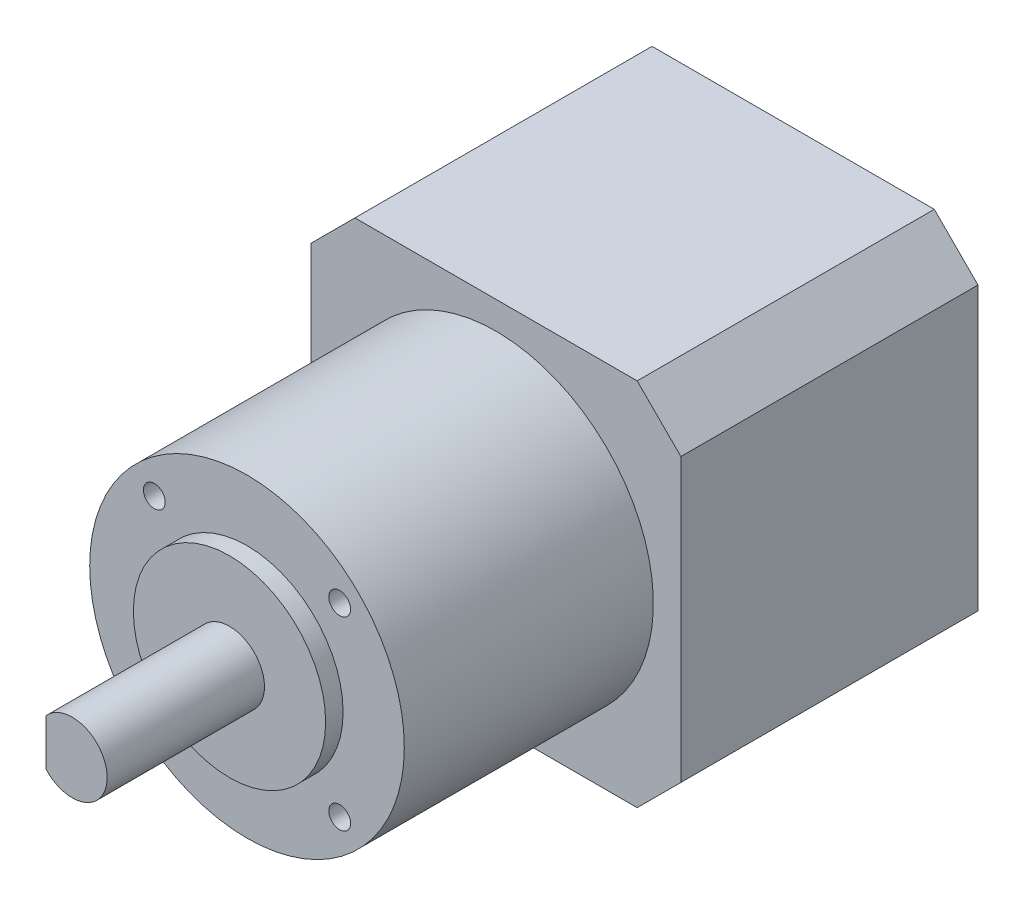
SolidWorks part; units mm, degrees
ref_plane "前视基准面" through (0, 0, 0) normal (0, 0, 1) x (1, 0, 0)
ref_plane "上视基准面" through (0, 0, 0) normal (0, 1, 0) x (1, 0, 0)
ref_plane "右视基准面" through (0, 0, 0) normal (1, 0, 0) x (0, 0, -1)
sketch "草图1" plane through (0, 0, 0) normal (0, 0, 1) x (1, 0, 0)
  line L0 (-21.15, 16.15) -> (-16.15, 21.15)
  line L1 (-16.15, -21.15) -> (16.15, -21.15)
  line L2 (-21.15, -16.15) -> (-21.15, 16.15)
  line L3 (-16.15, 21.15) -> (16.15, 21.15)
  line L4 (21.15, -16.15) -> (21.15, 16.15)
  line L5 (-21.15, -21.15) -> (21.15, 21.15) construction
  line L6 (-21.15, 21.15) -> (21.15, -21.15) construction
  line L7 (16.15, 21.15) -> (21.15, 16.15)
  line L8 (-21.15, -16.15) -> (-16.15, -21.15)
  line L9 (16.15, -21.15) -> (21.15, -16.15)
  point P0 (0, 0)
  dimension "D1" = 42.3
extrude "凸台-拉伸1" add sketch "草图1" along normal blind 34
sketch "草图2" plane through (0, 0, 34) normal (0, 0, 1) x (1, 0, 0)
  circle A0 centre (0, 0) radius 18
  dimension "D1" = 36
extrude "凸台-拉伸2" add sketch "草图2" along normal blind 28.5
sketch "草图3" plane through (0, 0, 62.5) normal (0, 0, 1) x (1, 0, 0)
  circle A0 centre (0, 0) radius 11
  dimension "D1" = 22
extrude "凸台-拉伸3" add sketch "草图3" along normal blind 2
sketch "草图4" plane through (0, 0, 64.5) normal (0, 0, 1) x (1, 0, 0)
  circle A0 centre (0, 0) radius 4
  dimension "D1" = 8
extrude "凸台-拉伸4" add sketch "草图4" along normal blind 18
sketch "草图5" plane through (0, 0, 82.5) normal (0, 0, 1) x (1, 0, 0)
  line L0 (-3, 5.3779) -> (-3, -8.0729)
  line L1 (-3, -8.0729) -> (-11.0943, -8.0729)
  line L2 (-11.0943, -8.0729) -> (-11.0943, 5.3779)
  line L3 (-11.0943, 5.3779) -> (-3, 5.3779)
  dimension "D1" = 3
extrude "切除-拉伸1" cut sketch "草图5" against normal blind 15
sketch "草图6" plane through (0, 0, 62.5) normal (0, 0, 1) x (1, 0, 0)
  line L0 (-10.6066, 10.6066) -> (10.6066, 10.6066) construction
  line L1 (10.6066, 10.6066) -> (10.6066, -10.6066) construction
  line L2 (10.6066, -10.6066) -> (-10.6066, -10.6066) construction
  line L3 (-10.6066, -10.6066) -> (-10.6066, 10.6066) construction
  line L4 (-10.6066, 10.6066) -> (10.6066, -10.6066) construction
  circle A0 centre (-10.6066, 10.6066) radius 1
  circle A1 centre (10.6066, 10.6066) radius 1
  circle A2 centre (-10.6066, -10.6066) radius 1
  circle A3 centre (10.6066, -10.6066) radius 1
  dimension "D2" = 2
  dimension "D1" = 30
extrude "切除-拉伸2" cut sketch "草图6" against normal blind 5
hole_wizard "M3 螺纹孔1" positions "草图7" profile "草图8" tap size "M3" standard "GB"
sketch "草图7" plane through (0, 0, 62.5) normal (0, 0, 1) x (1, 0, 0)
  point P0 (-10.6066, 10.6066)
  point P3 (10.6066, 10.6066)
  point P6 (-10.6066, -10.6066)
  point P9 (10.6066, -10.6066)
cosmetic thread "孔螺蚊线1" parameters "D1"=6, "D2"=3
cosmetic thread "孔螺蚊线2" parameters "D1"=6, "D2"=3
cosmetic thread "孔螺蚊线3" parameters "D1"=6, "D2"=3
cosmetic thread "孔螺蚊线4" parameters "D1"=6, "D2"=3
sketch "草图8" plane through (-10.6066, 10.6066, 62.5) normal (1, 0, 0) x (0, -1, 0)
  line L0 (0, 0) -> (0, 8.2511)
  line L1 (0, 8.2511) -> (1.25, 7.5)
  line L2 (1.25, 7.5) -> (1.25, 0)
  line L5 (1.25, 0) -> (0, 0)
  line L10 (0, 8.2511) -> (-1.25, 7.5) construction
  line L11 (0, -6.35) -> (0, 107.95) construction
  dimension "螺纹孔钻头直径" = 2.5
  dimension "螺纹孔钻头深度" = 7.5
  dimension "导头角度" = 118
